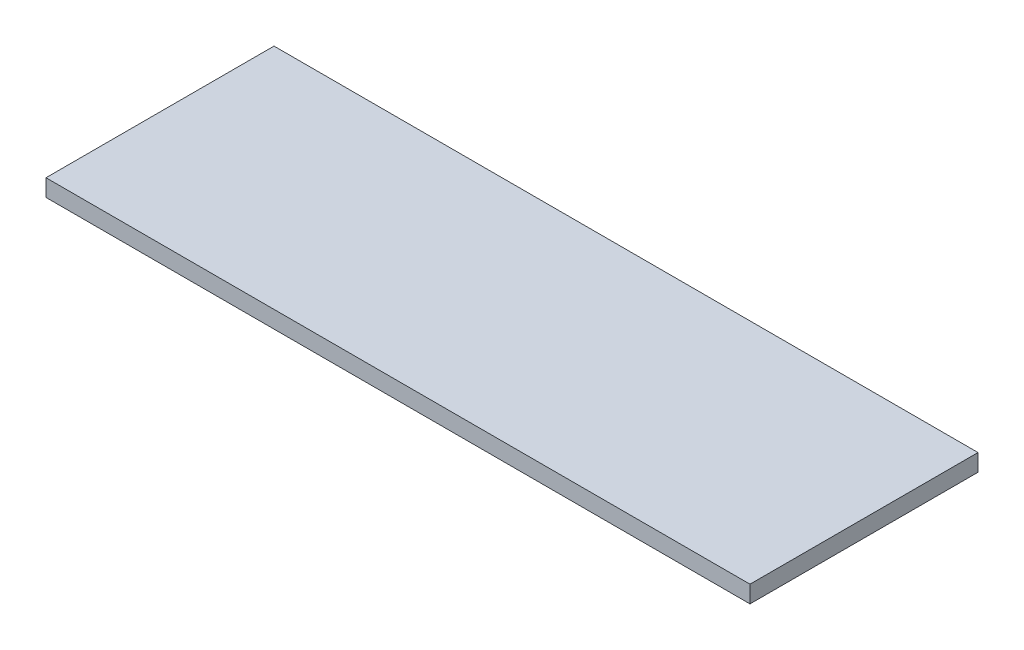
SolidWorks part; units mm, degrees
ref_plane "Front Plane" through (0, 0, 0) normal (0, 0, 1) x (1, 0, 0)
ref_plane "Top Plane" through (0, 0, 0) normal (0, 1, 0) x (1, 0, 0)
ref_plane "Right Plane" through (0, 0, 0) normal (1, 0, 0) x (0, 0, -1)
sketch "Sketch1" plane through (0, 0, 0) normal (0, 1, 0) x (1, 0, 0)
  line L1 (0, 0) -> (247, 0)
  line L2 (0, 0) -> (0, 80)
  line L3 (0, 80) -> (247, 80)
  line L4 (247, 0) -> (247, 80)
  dimension "D1" = 80
  dimension "D2" = 247
extrude "Boss-Extrude1" add sketch "Sketch1" along normal blind 6
